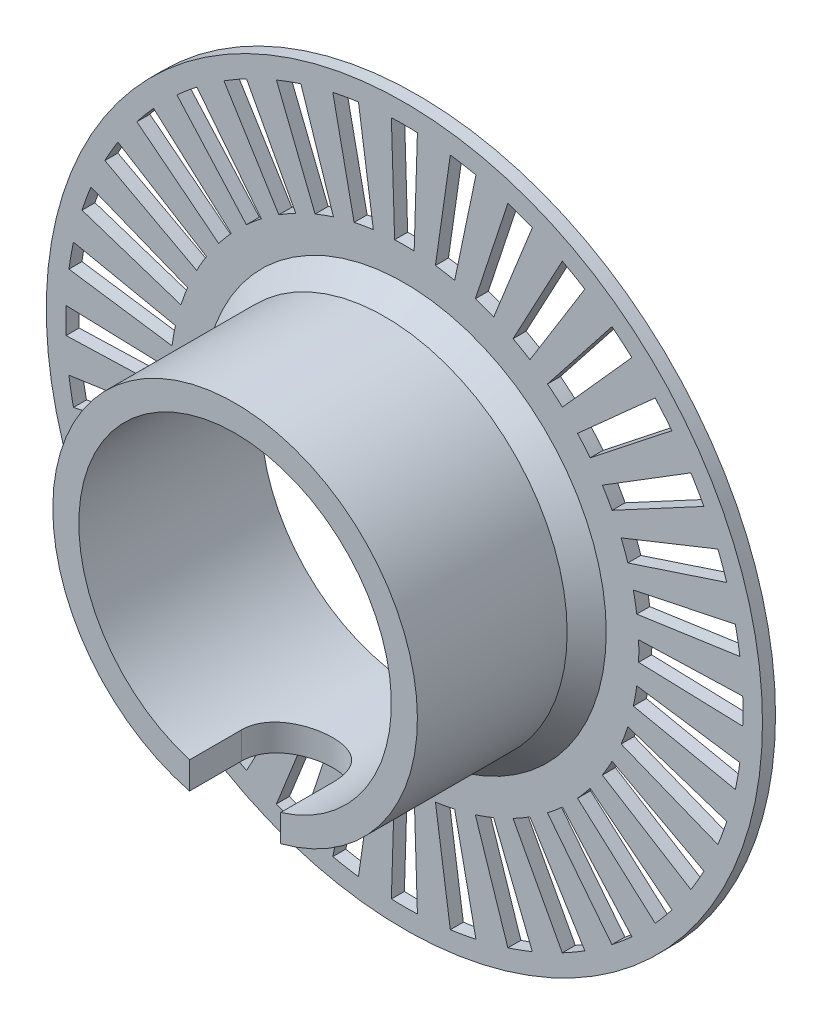
SolidWorks part; units mm, degrees
ref_plane "Front Plane" through (0, 0, 0) normal (0, 0, 1) x (1, 0, 0)
ref_plane "Top Plane" through (0, 0, 0) normal (0, 1, 0) x (1, 0, 0)
ref_plane "Right Plane" through (0, 0, 0) normal (1, 0, 0) x (0, 0, -1)
sketch "Sketch1" plane through (0, 0, 0) normal (0, 0, 1) x (1, 0, 0)
  circle A0 centre (0, 0) radius 27.5
  circle A1 centre (0, 0) radius 12
  dimension "D1" = 24
  dimension "D2" = 55
extrude "Boss-Extrude1" add sketch "Sketch1" along normal blind 1
sketch "Sketch3" plane through (0, 0, 1) normal (0, 0, 1) x (1, 0, 0)
  line L0 (0, 18) -> (0, 26) construction
  line L1 (0, 18) -> (0, 0) construction
  line L2 (-1, 25.9808) -> (-0.75, 17.9844)
  line L3 (1, 25.9808) -> (0.75, 17.9844)
  arc A0 (0.75, 17.9844) -> (-0.75, 17.9844) centre (0, 0) ccw
  arc A1 (1, 25.9808) -> (-1, 25.9808) centre (0, 0) ccw
  point P8 (0, 18)
  point P9 (0, 26)
  dimension "D1" = 8
  dimension "D2" = 18
  dimension "D3" = 1.5
  dimension "D4" = 2
extrude "Cut-Extrude1" cut sketch "Sketch3" against normal blind 1
pattern_circular "CirPattern1" count 36 every 10 about axis through (0, 0, 0) along (0, 0, 1) of "Cut-Extrude1"
sketch "Sketch4" plane through (0, 0, 1) normal (0, 0, 1) x (1, 0, 0)
  circle A0 centre (0, 0) radius 12
  circle A1 centre (0, 0) radius 14
  dimension "D1" = 28
extrude "Boss-Extrude2" add sketch "Sketch4" along normal blind 13
sketch "Sketch5" plane through (0, 0, 0) normal (0, 1, 0) x (1, 0, 0)
  line L0 (0, 0) -> (0, -10) construction
  line L1 (-3.5, -10) -> (-3.5, -14)
  line L2 (-14, -14) -> (14, -14) construction
  line L3 (-3.5, -14) -> (3.5, -14)
  line L4 (3.5, -14) -> (3.5, -10)
  arc A0 (3.5, -10) -> (-3.5, -10) centre (0, -10) ccw
  dimension "D1" = 10
  dimension "D2" = 7
extrude "Cut-Extrude2" cut sketch "Sketch5" against normal through all
chamfer "Chamfer1" distance 1.5 angle 45 1 edges at (14, 0, 1)
